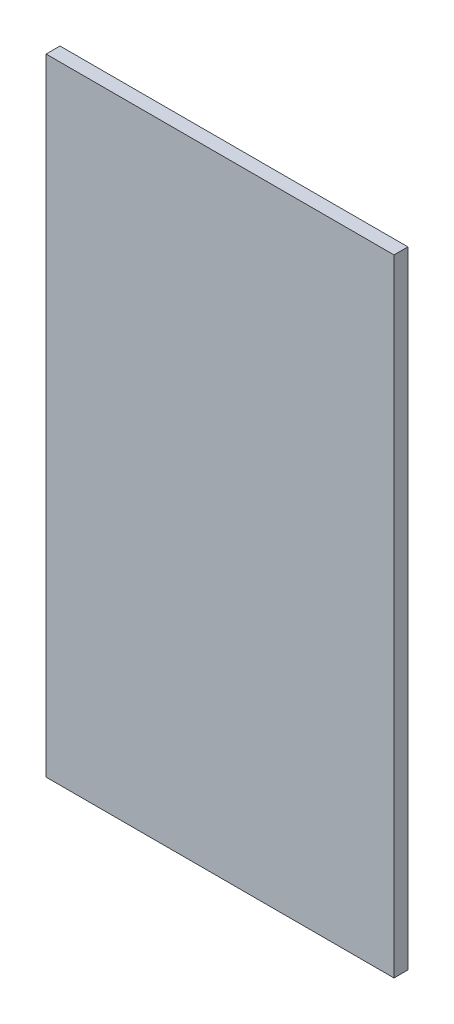
SolidWorks part; units mm, degrees
ref_plane "Ön Düzlem" through (0, 0, 0) normal (0, 0, 1) x (1, 0, 0)
ref_plane "Üst Düzlem" through (0, 0, 0) normal (0, 1, 0) x (1, 0, 0)
ref_plane "Sağ Düzlem" through (0, 0, 0) normal (1, 0, 0) x (0, 0, -1)
sketch "Sketch1" plane through (0, 0, 0) normal (0, 0, 1) x (1, 0, 0)
  line L1 (-250, -450) -> (250, -450)
  line L2 (-250, -450) -> (-250, 450)
  line L3 (-250, 450) -> (250, 450)
  line L4 (250, -450) -> (250, 450)
  line L5 (-250, -450) -> (250, 450) construction
  line L6 (-250, 450) -> (250, -450) construction
  point P0 (0, 0)
  dimension "D1" = 900
  dimension "D2" = 500
extrude "Boss-Extrude1" add sketch "Sketch1" along normal blind 20
